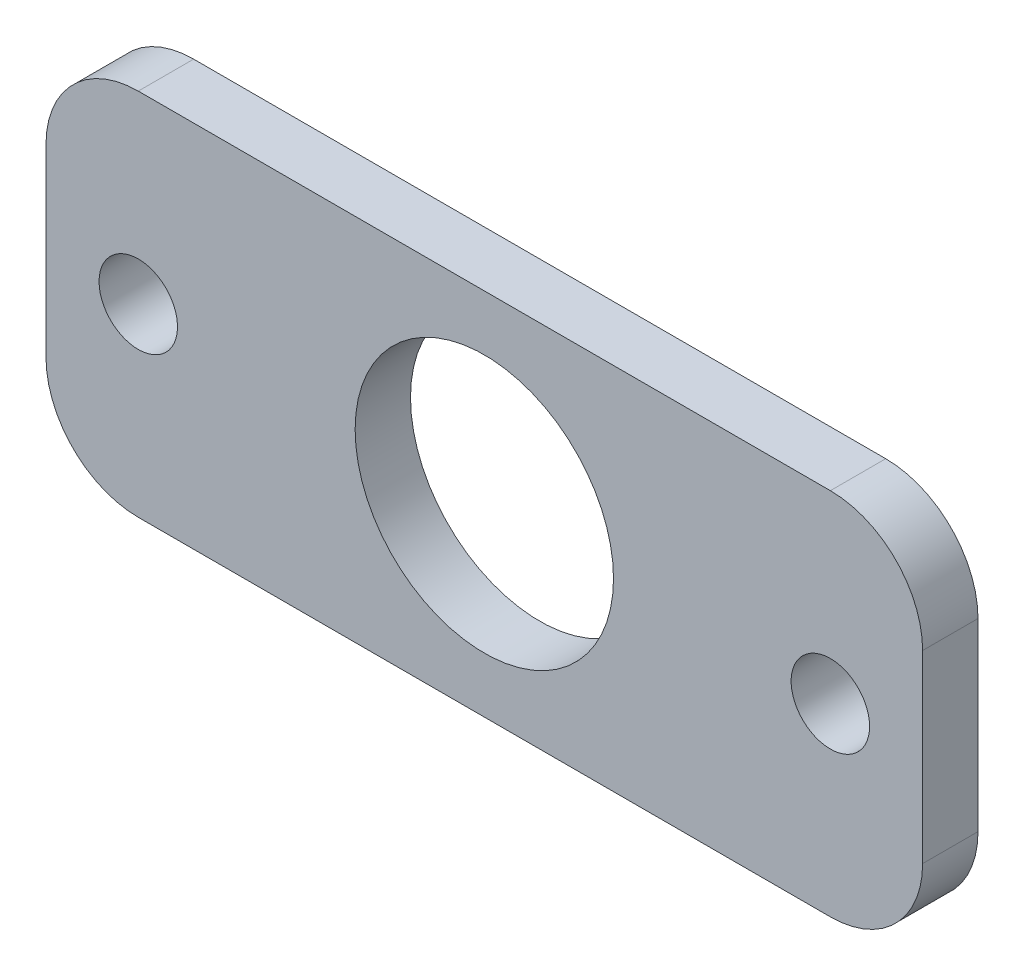
SolidWorks part; units mm, degrees
material "Plain Carbon Steel"
ref_plane "Front Plane" through (0, 0, 0) normal (0, 0, 1) x (1, 0, 0)
ref_plane "Top Plane" through (0, 0, 0) normal (0, 1, 0) x (1, 0, 0)
ref_plane "Right Plane" through (0, 0, 0) normal (1, 0, 0) x (0, 0, -1)
sketch "Sketch1" plane through (0, 0, 0) normal (0, 0, 1) x (1, 0, 0)
  line L0 (-420, 0) -> (420, 0) construction
  line L1 (395, 0) -> (300, 0)
  line L2 (395, 0) -> (395, -40)
  line L3 (395, -40) -> (300, -40)
  line L4 (300, 0) -> (300, -40)
  line L5 (-420, -40) -> (420, -40) construction
  line L6 (347.5, -20) -> (395, -20) construction
  line L7 (347.5, -20) -> (347.5, -40) construction
  line L8 (395, 0) -> (395, 6) construction
  line L9 (300, 0) -> (300, 6) construction
  line L10 (300, -20) -> (347.5, -20) construction
  circle A0 centre (347.5, -20) radius 14
  circle A2 centre (347.5, -20) radius 9.5 construction
  circle A3 centre (385, -20) radius 4.25
  circle A4 centre (310, -20) radius 4.25
  dimension "D1" = 28
  dimension "D2" = 8.5
  dimension "D3" = 10
extrude "Boss-Extrude1" add sketch "Sketch1" along normal blind 6
fillet "Fillet1" radius 10 4 edges at (395, 0, 3) (395, -40, 3) (300, -40, 3) (300, 0, 3)
